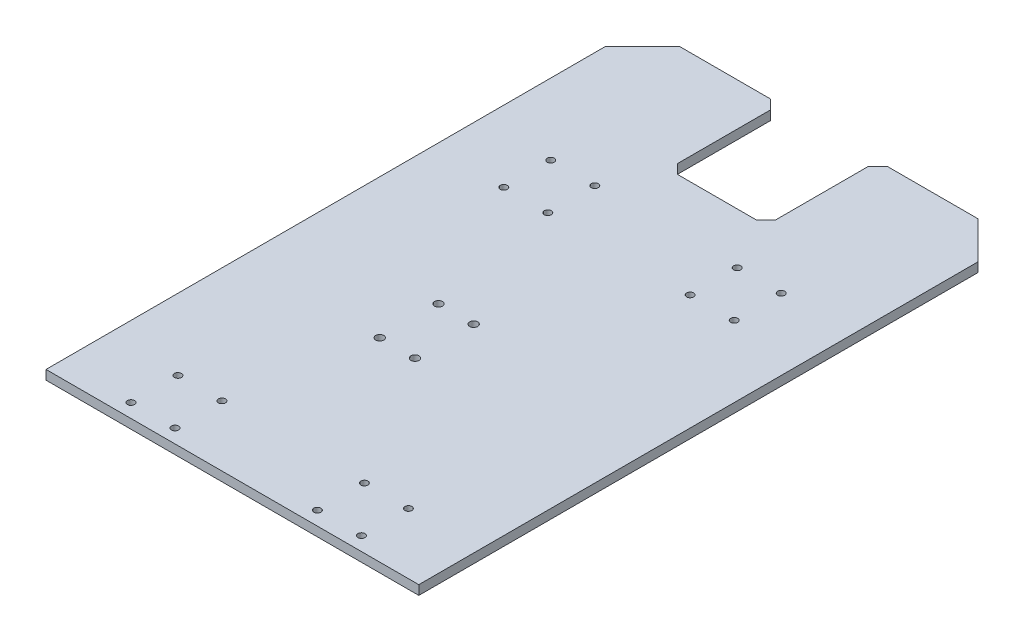
SolidWorks part; units mm, degrees
ref_plane "Front Plane" through (0, 0, 0) normal (0, 0, 1) x (1, 0, 0)
ref_plane "Top Plane" through (0, 0, 0) normal (0, 1, 0) x (1, 0, 0)
ref_plane "Right Plane" through (0, 0, 0) normal (1, 0, 0) x (0, 0, -1)
sketch "Sketch2" plane through (0, 0, 0) normal (0, 1, 0) x (1, 0, 0)
  line L1 (-127, 152.4) -> (127, 152.4)
  line L2 (-127, 152.4) -> (-127, -152.4)
  line L3 (-127, -152.4) -> (127, -152.4)
  line L4 (127, 152.4) -> (127, -152.4)
  line L5 (-127, 152.4) -> (127, -152.4) construction
  line L6 (-127, -152.4) -> (127, 152.4) construction
  point P0 (0, 0)
  dimension "D1" = 304.8
  dimension "D2" = 254
extrude "Boss-Extrude1" add sketch "Sketch2" along normal blind 6.35
ref_plane "Top" through (0, 0, -152.4) normal (0, 0, -1) x (-1, 0, 0)
hole_wizard "M4 Clearance Hole1" positions "Sketch4" profile "Sketch5" hole size "M4" standard "ANSI Metric" end condition up to next
sketch "Sketch4" plane through (0, 6.35, 0) normal (0, 1, 0) x (1, 0, 0)
  circle A0 centre (78.5, -111) radius 2.1 construction
  circle A1 centre (48.5, -111) radius 2.1 construction
  circle A2 centre (48.5, -143) radius 2.1 construction
  circle A3 centre (78.5, -143) radius 2.1 construction
  circle A4 centre (-48.5, -111) radius 2.1 construction
  circle A5 centre (-48.5, -143) radius 2.1 construction
  circle A6 centre (-78.5, -111) radius 2.1 construction
  circle A7 centre (-78.5, -143) radius 2.1 construction
  circle A8 centre (78.5, 143) radius 2.1 construction
  circle A9 centre (78.5, 111) radius 2.1 construction
  circle A10 centre (48.5, 143) radius 2.1 construction
  circle A11 centre (48.5, 111) radius 2.1 construction
  circle A12 centre (-48.5, 143) radius 2.1 construction
  circle A13 centre (-48.5, 111) radius 2.1 construction
  circle A14 centre (-78.5, 143) radius 2.1 construction
  circle A15 centre (-78.5, 111) radius 2.1 construction
  circle A16 centre (78.5, -111) radius 2.1 construction
  circle A17 centre (48.5, -111) radius 2.1 construction
  circle A18 centre (48.5, -143) radius 2.1 construction
  circle A19 centre (78.5, -143) radius 2.1 construction
  circle A20 centre (-48.5, -111) radius 2.1 construction
  circle A21 centre (-48.5, -143) radius 2.1 construction
  circle A22 centre (-78.5, -111) radius 2.1 construction
  circle A23 centre (-78.5, -143) radius 2.1 construction
  circle A24 centre (78.5, 143) radius 2.1 construction
  circle A25 centre (78.5, 111) radius 2.1 construction
  circle A26 centre (48.5, 143) radius 2.1 construction
  circle A27 centre (48.5, 111) radius 2.1 construction
  circle A28 centre (-48.5, 143) radius 2.1 construction
  circle A29 centre (-48.5, 111) radius 2.1 construction
  circle A30 centre (-78.5, 143) radius 2.1 construction
  circle A31 centre (-78.5, 111) radius 2.1 construction
  point P1 (78.5, -111)
  point P3 (48.5, -111)
  point P5 (48.5, -143)
  point P7 (78.5, -143)
  point P9 (-48.5, -111)
  point P11 (-48.5, -143)
  point P13 (-78.5, -111)
  point P15 (-78.5, -143)
  point P17 (78.5, 143)
  point P19 (78.5, 111)
  point P21 (48.5, 143)
  point P23 (48.5, 111)
  point P25 (-48.5, 143)
  point P27 (-48.5, 111)
  point P29 (-78.5, 143)
  point P31 (-78.5, 111)
sketch "Sketch5" plane through (78.5, 6.35, 111) normal (1, 0, 0) x (0, 0, 1)
  line L0 (0, 0) -> (0, 6.35)
  line L1 (0, 6.35) -> (2.4, 6.35)
  line L2 (2.4, 6.35) -> (2.4, 0)
  line L5 (2.4, 0) -> (0, 0)
  line L11 (0, -6.35) -> (0, 107.95) construction
  dimension "Thru Hole Dia." = 4.8
  dimension "Thru Hole Depth" = 6.35
sketch "Sketch6" plane through (0, 0, -152.4) normal (0, 0, -1) x (-1, 0, 0)
  line L4 (-127, 0) -> (127, 0)
  line L5 (127, 0) -> (127, 6.35)
  line L6 (127, 6.35) -> (-127, 6.35)
  line L7 (-127, 6.35) -> (-127, 0)
  line L8 (-127, 0) -> (127, 0)
  line L9 (127, 0) -> (127, 6.35)
  line L10 (127, 6.35) -> (-127, 6.35)
  line L11 (-127, 6.35) -> (-127, 0)
  dimension "D1" = 0
extrude "Boss-Extrude2" add sketch "Sketch6" along normal blind 101.6
chamfer "Chamfer1" distance 25.4 angle 45 2 edges at (-127, 3.175, -254) (127, 3.175, -254)
sketch "Sketch7" plane through (0, 6.35, 0) normal (0, 1, 0) x (1, 0, 0)
  line L0 (-101.6, 254) -> (101.6, 254) construction
  line L1 (-33.3375, 254) -> (33.3375, 254)
  line L2 (-33.3375, 254) -> (-33.3375, 177.8)
  line L3 (-33.3375, 177.8) -> (33.3375, 177.8)
  line L4 (33.3375, 254) -> (33.3375, 177.8)
  line L5 (-33.3375, 254) -> (33.3375, 177.8) construction
  line L6 (-33.3375, 177.8) -> (33.3375, 254) construction
  line L7 (-101.6, 254) -> (101.6, 254) construction
  point P0 (0, 215.9)
  point P9 (0, 254)
  dimension "D1" = 66.675
  dimension "D2" = 76.2
extrude "Cut-Extrude1" cut sketch "Sketch7" against normal through all
chamfer "Chamfer2" distance 6.35 angle 45 4 edges at (33.3375, 3.175, -177.8) (-33.3375, 3.175, -177.8) (33.3375, 3.175, -254) (-33.3375, 3.175, -254)
hole_wizard "M5 Clearance Hole1" positions "Sketch8" profile "Sketch9" hole size "M5" standard "ANSI Metric" end condition through all
sketch "Sketch8" plane through (0, 6.35, 0) normal (0, 1, 0) x (1, 0, 0)
  circle A0 centre (-8, 20) radius 2.1 construction
  circle A1 centre (-32, 20) radius 2.1 construction
  circle A2 centre (-32, -20) radius 2.1 construction
  circle A3 centre (-8, -20) radius 2.1 construction
  circle A4 centre (-8, 20) radius 2.1 construction
  circle A5 centre (-32, 20) radius 2.1 construction
  circle A6 centre (-32, -20) radius 2.1 construction
  circle A7 centre (-8, -20) radius 2.1 construction
  point P17 (-8, 20)
  point P20 (-32, 20)
  point P23 (-32, -20)
  point P26 (-8, -20)
sketch "Sketch9" plane through (-8, 6.35, 20) normal (1, 0, 0) x (0, 0, 1)
  line L0 (0, 0) -> (0, 6.35)
  line L1 (0, 6.35) -> (2.75, 6.35)
  line L2 (2.75, 6.35) -> (2.75, 0)
  line L5 (2.75, 0) -> (0, 0)
  line L11 (0, -6.35) -> (0, 107.95) construction
  dimension "Thru Hole Dia." = 5.5
  dimension "Thru Hole Depth" = 6.35
